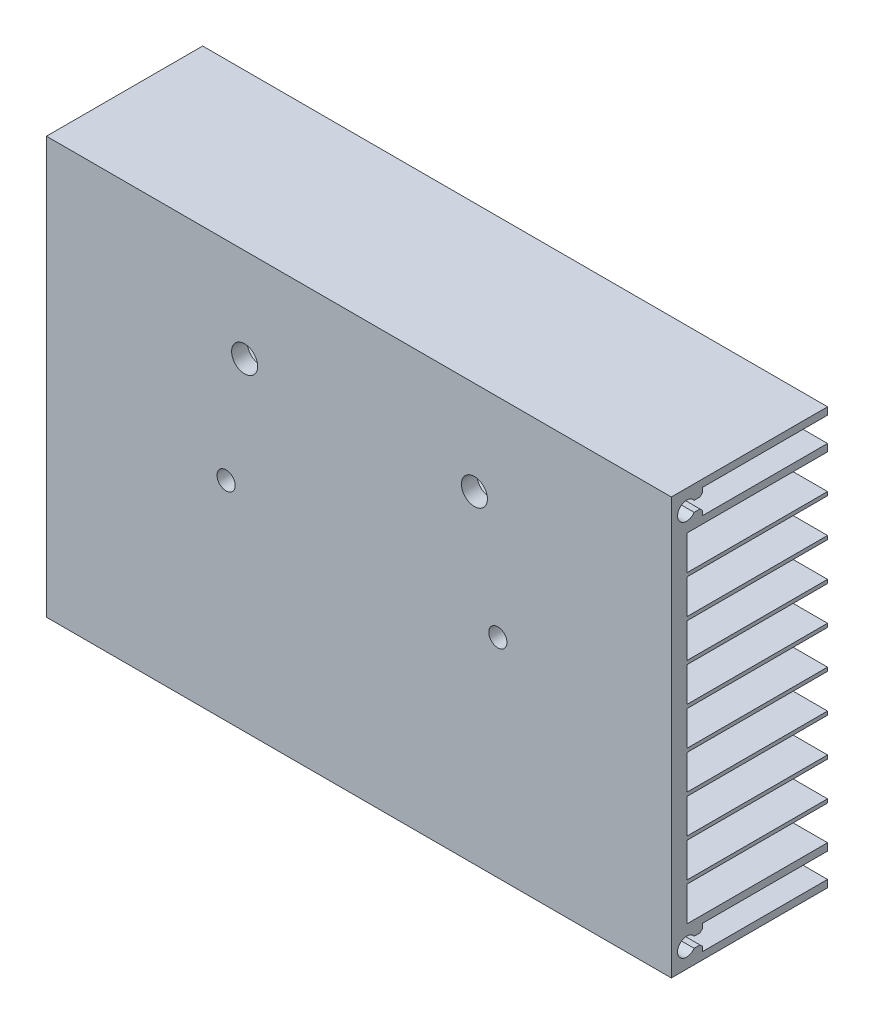
SolidWorks part; units mm, degrees
ref_plane "Piano frontale" through (0, 0, 0) normal (0, 0, 1) x (1, 0, 0)
ref_plane "Piano superiore" through (0, 0, 0) normal (0, 1, 0) x (1, 0, 0)
ref_plane "Piano destro" through (0, 0, 0) normal (1, 0, 0) x (0, 0, -1)
sketch "Schizzo1" plane through (0, 0, 0) normal (0, 0, 1) x (1, 0, 0)
  line L1 (-60, 40) -> (60, 40)
  line L2 (-60, 40) -> (-60, -40)
  line L3 (-60, -40) -> (60, -40)
  line L4 (60, 40) -> (60, -40)
  line L5 (-60, 40) -> (60, -40) construction
  line L6 (-60, -40) -> (60, 40) construction
  point P0 (0, 0)
  dimension "D1" = 120
  dimension "D2" = 80
extrude "Estrusione-Estrusione1" add sketch "Schizzo1" along normal blind 30
sketch "Schizzo2" plane through (-60, 0, 0) normal (-1, 0, 0) x (0, 0, 1)
  line L0 (0, 40) -> (0, -40) construction
  line L1 (0, -32.5) -> (27, -32.5)
  line L2 (0, -32.5) -> (0, -25.9)
  line L3 (0, -25.9) -> (27, -25.9)
  line L4 (27, -32.5) -> (27, -25.9)
  line L5 (30, -40) -> (0, -40) construction
  dimension "D1" = 6.6
  dimension "D2" = 27
  dimension "D3" = 7.5
extrude "Taglio-Estrusione1" cut sketch "Schizzo2" against normal through all
pattern_linear "Ripetizione a L1" count 9 spacing 7.3 along (0, 1, 0) of "Taglio-Estrusione1"
sketch "Schizzo3" plane through (60, 0, 0) normal (1, 0, 0) x (0, 0, -1)
  line L0 (0, 0) -> (-35.3514, 0) construction
  line L2 (0, -36.25) -> (-24, -36.25) construction
  line L3 (0, -40) -> (0, -32.5) construction
  line L4 (-24, 38.6) -> (0, 33.9) construction
  line L9 (-24, 33.9) -> (0, 38.6) construction
  line L10 (0, 36.25) -> (-24, 36.25) construction
  line L11 (-24, -33.9) -> (0, -33.9)
  line L12 (-24, -33.9) -> (-24, -38.6)
  line L13 (-24, -38.6) -> (0, -38.6)
  line L14 (0, -33.9) -> (0, -38.6)
  line L15 (-24, -33.9) -> (0, -38.6) construction
  line L16 (-24, -38.6) -> (0, -33.9) construction
  line L17 (0, 33.9) -> (0, 38.6)
  line L18 (-24, 38.6) -> (0, 38.6)
  line L19 (-24, 33.9) -> (-24, 38.6)
  line L20 (-24, 33.9) -> (0, 33.9)
  point P12 (-12, 36.25)
  point P13 (-12, -36.25)
  dimension "D1" = 24
  dimension "D2" = 4.7
extrude "Taglio-Estrusione2" cut sketch "Schizzo3" against normal through all
sketch "Schizzo4" plane through (60, 0, 0) normal (1, 0, 0) x (0, 0, -1)
  line L0 (-27.05, 36.25) -> (-24, 36.25) construction
  line L1 (-24, 38.6) -> (-24, 33.9) construction
  line L3 (-27.05, 35.25) -> (-24, 35.25)
  line L4 (-27.05, 35.25) -> (-27.05, 37.25)
  line L5 (-27.05, 37.25) -> (-24, 37.25)
  line L6 (-24, 35.25) -> (-24, 37.25)
  line L7 (-27.05, 35.25) -> (-24, 37.25) construction
  line L8 (-27.05, 37.25) -> (-24, 35.25) construction
  line L10 (0, 0) -> (-43.7391, 0) construction
  line L11 (-27.05, -37.25) -> (-24, -35.25) construction
  line L12 (-27.05, -35.25) -> (-24, -37.25) construction
  line L13 (-27.05, -36.25) -> (-24, -36.25) construction
  line L14 (-24, -35.25) -> (-24, -37.25)
  line L15 (-27.05, -37.25) -> (-24, -37.25)
  line L16 (-27.05, -35.25) -> (-27.05, -37.25)
  line L17 (-27.05, -35.25) -> (-24, -35.25)
  circle A0 centre (-27.05, 36.25) radius 1.75
  circle A1 centre (-27.05, -36.25) radius 1.75
  point P2 (-25.525, 36.25)
  point P20 (-25.525, -36.25)
  line M2 (-24, 33.9) -> (-24, 38.6)
  line M10 (-24, -38.6) -> (-24, -33.9)
  dimension "D1" = 1.3
  dimension "D2" = 3.5
  dimension "D3" = 2
extrude "Taglio-Estrusione3" cut sketch "Schizzo4" against normal through all contours A0 L3 L5 M2 | L3 A0 L5 L4 | L5 A0 L3 L4 | A1 L15 L16 L17 | A1 L17 L16 L15 | L17 A1 L15 M10
chamfer "Smusso1" distance 0.5 angle 45 4 edges at (0, 35.25, 24) (0, 37.25, 24) (0, -37.25, 24) (0, -35.25, 24)
sketch "Schizzo5" plane through (0, 0, 30) normal (0, 0, 1) x (1, 0, 0)
  line L0 (-30, 22) -> (-19.77, 22) construction
  line L1 (19.77, 22) -> (30, 22) construction
  circle A0 centre (-25.5, 0) radius 1.75
  circle A1 centre (26.6862, 0) radius 1.75
  circle A2 centre (-21.9446, 22) radius 2.5
  circle A3 centre (22.182, 22) radius 2.5
  dimension "D1" = 3.5
  dimension "D2" = 5
  dimension "D3" = 21.9446
  dimension "D4" = 22.182
extrude "Taglio-Estrusione4" cut sketch "Schizzo5" against normal blind 10
